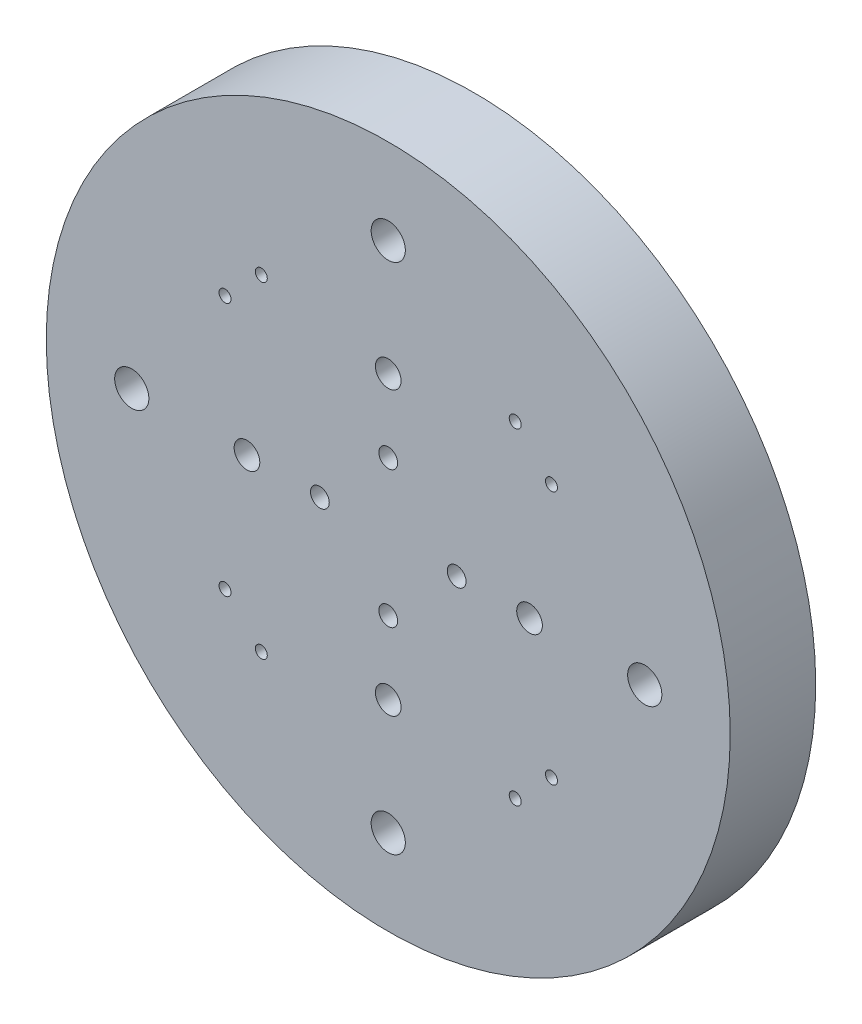
SolidWorks part; units mm, degrees
ref_plane "Front Plane" through (0, 0, 0) normal (0, 0, 1) x (1, 0, 0)
ref_plane "Top Plane" through (0, 0, 0) normal (0, 1, 0) x (1, 0, 0)
ref_plane "Right Plane" through (0, 0, 0) normal (1, 0, 0) x (0, 0, -1)
sketch "Sketch1" plane through (0, 0, 0) normal (0, 0, 1) x (1, 0, 0)
  circle A0 centre (0, 0) radius 40
extrude "Boss-Extrude1" add sketch "Sketch1" along normal blind 10
hole_wizard "Ø4.0 (4) Diameter Hole1" positions "Sketch5" profile "Sketch4" hole size "Ø4.0" standard "ANSI Metric"
sketch "Sketch5" plane through (0, 0, 10) normal (0, 0, 1) x (1, 0, 0)
  circle A0 centre (0, 0) radius 30
  point P0 (0, 30)
  point P2 (30, 0)
  point P4 (-30, 0)
  point P6 (0, -30)
sketch "Sketch4" plane through (0, 30, 10) normal (1, 0, 0) x (0, -1, 0)
  line L0 (0, 0) -> (0, 11.2017)
  line L1 (0, 11.2017) -> (2, 10)
  line L2 (2, 10) -> (2, 0)
  line L5 (2, 0) -> (0, 0)
  line L10 (0, 11.2017) -> (-2, 10) construction
  line L11 (0, -6.35) -> (0, 107.95) construction
  dimension "Hole Dia." = 4
  dimension "Hole Depth" = 10
  dimension "Drill Angle" = 118
hole_wizard "Ø2.2 (2.2) Diameter Hole1" positions "Sketch7" profile "Sketch6" hole size "Ø2.2" standard "ANSI Metric"
sketch "Sketch7" plane through (0, 0, 10) normal (0, 0, 1) x (1, 0, 0)
  circle A0 centre (0, 0) radius 8
  point P0 (0, 8)
  point P2 (0, -8)
  point P4 (-8, 0)
  point P6 (8, 0)
sketch "Sketch6" plane through (0, 8, 10) normal (1, 0, 0) x (0, -1, 0)
  line L0 (0, 0) -> (0, 10.6609)
  line L1 (0, 10.6609) -> (1.1, 10)
  line L2 (1.1, 10) -> (1.1, 0)
  line L5 (1.1, 0) -> (0, 0)
  line L10 (0, 10.6609) -> (-1.1, 10) construction
  line L11 (0, -6.35) -> (0, 107.95) construction
  dimension "Hole Dia." = 2.2
  dimension "Hole Depth" = 10
  dimension "Drill Angle" = 118
hole_wizard "Ø3.0 (3) Diameter Hole4" positions "Sketch9" profile "Sketch8" hole size "Ø3.0" standard "ANSI Metric"
sketch "Sketch9" plane through (0, 0, 10) normal (0, 0, 1) x (1, 0, 0)
  circle A0 centre (0, 0) radius 16.5245
  point P0 (0, -16.5245)
  point P2 (16.5245, 0)
  point P4 (0, 16.5245)
  point P6 (-16.5245, 0)
sketch "Sketch8" plane through (0, -16.5245, 10) normal (1, 0, 0) x (0, -1, 0)
  line L0 (0, 0) -> (0, 10.9013)
  line L1 (0, 10.9013) -> (1.5, 10)
  line L2 (1.5, 10) -> (1.5, 0)
  line L5 (1.5, 0) -> (0, 0)
  line L10 (0, 10.9013) -> (-1.5, 10) construction
  line L11 (0, -6.35) -> (0, 107.95) construction
  dimension "Hole Dia." = 3
  dimension "Hole Depth" = 10
  dimension "Drill Angle" = 118
sketch "Sketch10" plane through (0, 0, 10) normal (0, 0, 1) x (1, 0, 0)
  line L0 (0, 0) -> (-28.2843, -28.2843) construction
  line L1 (-28.2843, -28.2843) -> (33.8468, 33.8468) construction
  circle A0 centre (0, 0) radius 40 construction
hole_wizard "Ø1.4 (1.4) Diameter Hole1" positions "Sketch12" profile "Sketch11" hole size "Ø1.4" standard "ANSI Metric" end condition through all
sketch "Sketch12" plane through (0, 0, 10) normal (0, 0, 1) x (1, 0, 0)
  line L0 (-16.5245, 0) -> (-4.2426, -12.2818) construction
  line L2 (0, 0) -> (-28.2843, -28.2843) construction
  line L3 (-26.9569, -6.9842) -> (-9.097, -24.8441) construction
  point P0 (-14.8492, -19.0919)
  point P2 (-19.0919, -14.8492)
  dimension "D1" = 90
  dimension "D4" = 24
sketch "Sketch11" plane through (-14.8492, -19.0919, 10) normal (1, 0, 0) x (0, -1, 0)
  line L0 (0, 0) -> (0, 10)
  line L1 (0, 10) -> (0.7, 10)
  line L2 (0.7, 10) -> (0.7, 0)
  line L5 (0.7, 0) -> (0, 0)
  line L11 (0, -6.35) -> (0, 107.95) construction
  dimension "Thru Hole Dia." = 1.4
  dimension "Thru Hole Depth" = 10
pattern_circular "CirPattern1" count 4 over 360 about axis through (0, 0, 0) along (0, 0, 1) of "Ø1.4 (1.4) Diameter Hole1"
